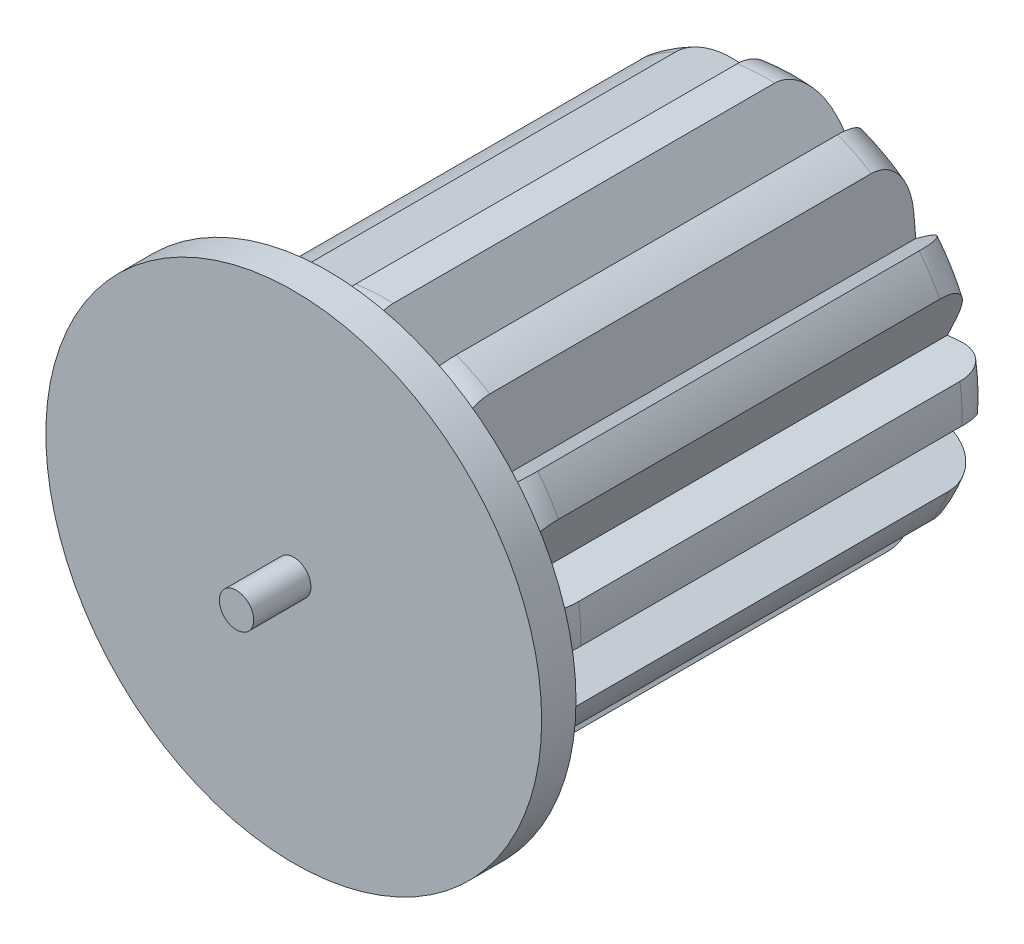
SolidWorks part; units mm, degrees
ref_plane "Front Plane" through (0, 0, 0) normal (0, 0, 1) x (1, 0, 0)
ref_plane "Top Plane" through (0, 0, 0) normal (0, 1, 0) x (1, 0, 0)
ref_plane "Right Plane" through (0, 0, 0) normal (1, 0, 0) x (0, 0, -1)
sketch "Sketch1" plane through (0, 0, 0) normal (0, 0, 1) x (1, 0, 0)
  circle A0 centre (0, 0) radius 102.5
  dimension "D1" = 205
extrude "Boss-Extrude1" add sketch "Sketch1" along normal blind 250
fillet "Fillet1" radius 30 1 edges at (102.5, 0, 250)
fillet "Fillet2" radius 20 1 edges at (102.5, 0, 0)
sketch "Sketch2" plane through (0, 0, 250) normal (0, 0, 1) x (1, 0, 0)
  line L0 (-114.2859, 121.8743) -> (-13.2185, 74.7458)
  line L1 (-13.2185, 74.7458) -> (-22.9377, 185.8371)
  line L2 (-22.9377, 185.8371) -> (-114.2859, 121.8743)
extrude "Cut-Extrude1" cut sketch "Sketch2" against normal blind 250
pattern_circular "CirPattern1" count 12 over 360 about axis through (0, 0, 0) along (0, 0, 1) of "Cut-Extrude1"
sketch "Sketch3" plane through (0, 0, 250) normal (0, 0, 1) x (1, 0, 0)
  circle A0 centre (0, 0) radius 130
  dimension "D1" = 260
extrude "Boss-Extrude2" add sketch "Sketch3" along normal blind 18
sketch "Sketch4" plane through (0, 0, 268) normal (0, 0, 1) x (1, 0, 0)
  circle A0 centre (0, 0) radius 9
  dimension "D1" = 18
extrude "Boss-Extrude3" add sketch "Sketch4" along normal blind 30
